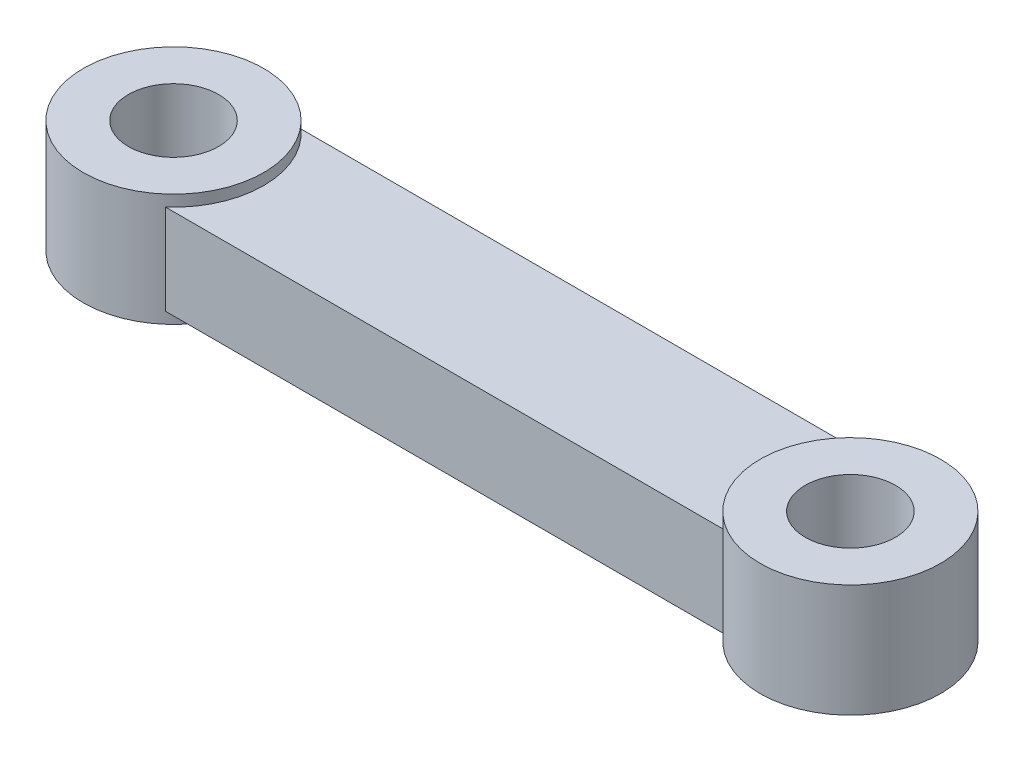
SolidWorks part; units mm, degrees
ref_plane "前视基准面" through (0, 0, 0) normal (0, 0, 1) x (1, 0, 0)
ref_plane "上视基准面" through (0, 0, 0) normal (0, 1, 0) x (1, 0, 0)
ref_plane "右视基准面" through (0, 0, 0) normal (1, 0, 0) x (0, 0, -1)
sketch "草图1" plane through (0, 0, 0) normal (0, 1, 0) x (1, 0, 0)
  circle A0 centre (0, 0) radius 4
  circle A1 centre (0, 0) radius 8
  circle A2 centre (60, 0) radius 4
  circle A3 centre (60, 0) radius 8
  dimension "D1" = 16
  dimension "D2" = 8
  dimension "D3" = 60
extrude "凸台-拉伸1" add sketch "草图1" along normal blind 10
sketch "草图2" plane through (0, 0, 0) normal (0, 1, 0) x (1, 0, 0)
  line L0 (0, 0) -> (60, 0) construction
  line L1 (5.2915, -6) -> (54.7085, -6)
  line L2 (5.2915, 6) -> (54.7085, 6)
  line L4 (0, 6) -> (60, 6) construction
  line L5 (0, -6) -> (60, -6) construction
  circle A0 centre (60, 0) radius 8 construction
  circle A1 centre (0, 0) radius 8 construction
  arc A2 (54.7085, 6) -> (54.7085, -6) centre (60, 0) ccw
  arc A3 (5.2915, -6) -> (5.2915, 6) centre (0, 0) ccw
  dimension "D1" = 6
  dimension "D2" = 6
extrude "凸台-拉伸2" add sketch "草图2" along normal blind 8 from offset 1
